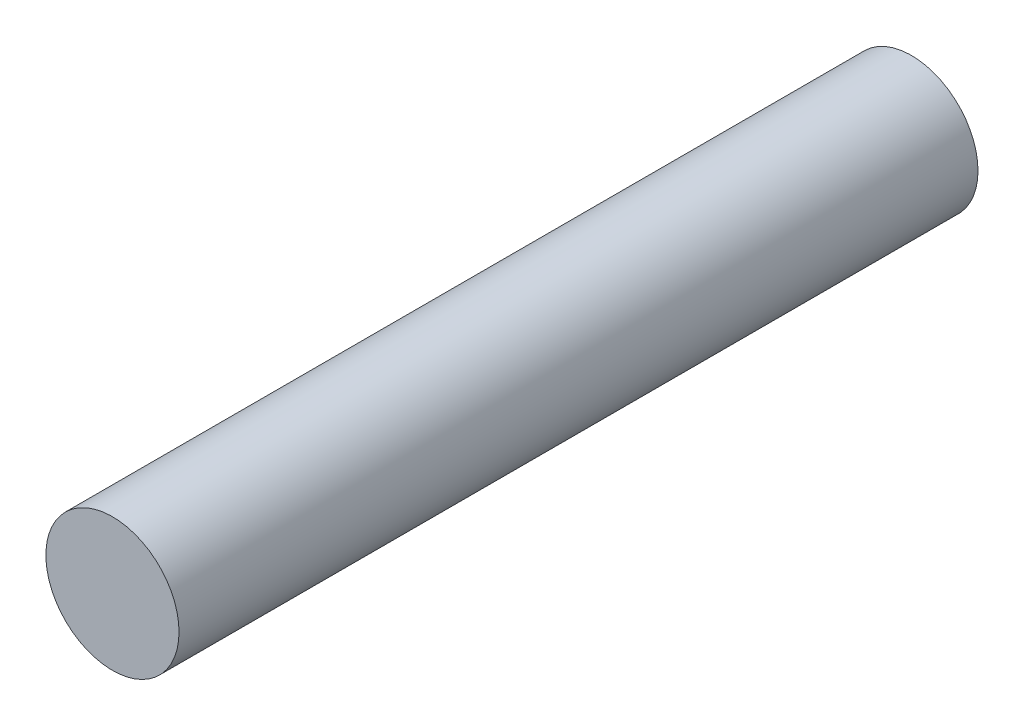
SolidWorks part; units mm, degrees
ref_plane "Front Plane" through (0, 0, 0) normal (0, 0, 1) x (1, 0, 0)
ref_plane "Top Plane" through (0, 0, 0) normal (0, 1, 0) x (1, 0, 0)
ref_plane "Right Plane" through (0, 0, 0) normal (1, 0, 0) x (0, 0, -1)
sketch "Sketch1" plane through (0, 0, 0) normal (0, 0, 1) x (1, 0, 0)
  circle A0 centre (0, 0) radius 0.5
extrude "Boss-Extrude1" add sketch "Sketch1" along normal blind 6
